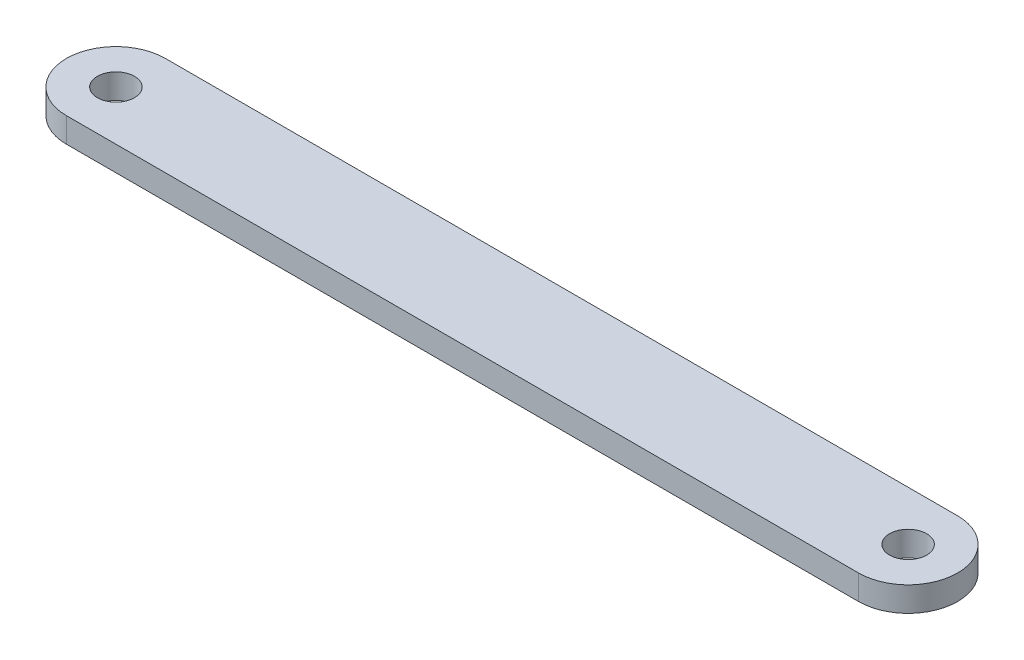
SolidWorks part; units mm, degrees
ref_plane "Front Plane" through (0, 0, 0) normal (0, 0, 1) x (1, 0, 0)
ref_plane "Top Plane" through (0, 0, 0) normal (0, 1, 0) x (1, 0, 0)
ref_plane "Right Plane" through (0, 0, 0) normal (1, 0, 0) x (0, 0, -1)
sketch "Sketch1" plane through (0, 0, 0) normal (0, 1, 0) x (1, 0, 0)
  line L0 (-101.6, 0) -> (101.6, 0) construction
  line L1 (-101.6, 12.7) -> (101.6, 12.7)
  line L2 (-101.6, -12.7) -> (101.6, -12.7)
  arc A0 (-101.6, 12.7) -> (-101.6, -12.7) centre (-101.6, 0) ccw
  arc A1 (101.6, -12.7) -> (101.6, 12.7) centre (101.6, 0) ccw
  circle A2 centre (-101.6, 0) radius 4.7625
  circle A3 centre (101.6, 0) radius 4.7625
  point P3 (0, 0)
  dimension "D3" = 9.525
  dimension "D1" = 25.4
  dimension "D2" = 203.2
extrude "Boss-Extrude1" add sketch "Sketch1" along normal blind 6.35
